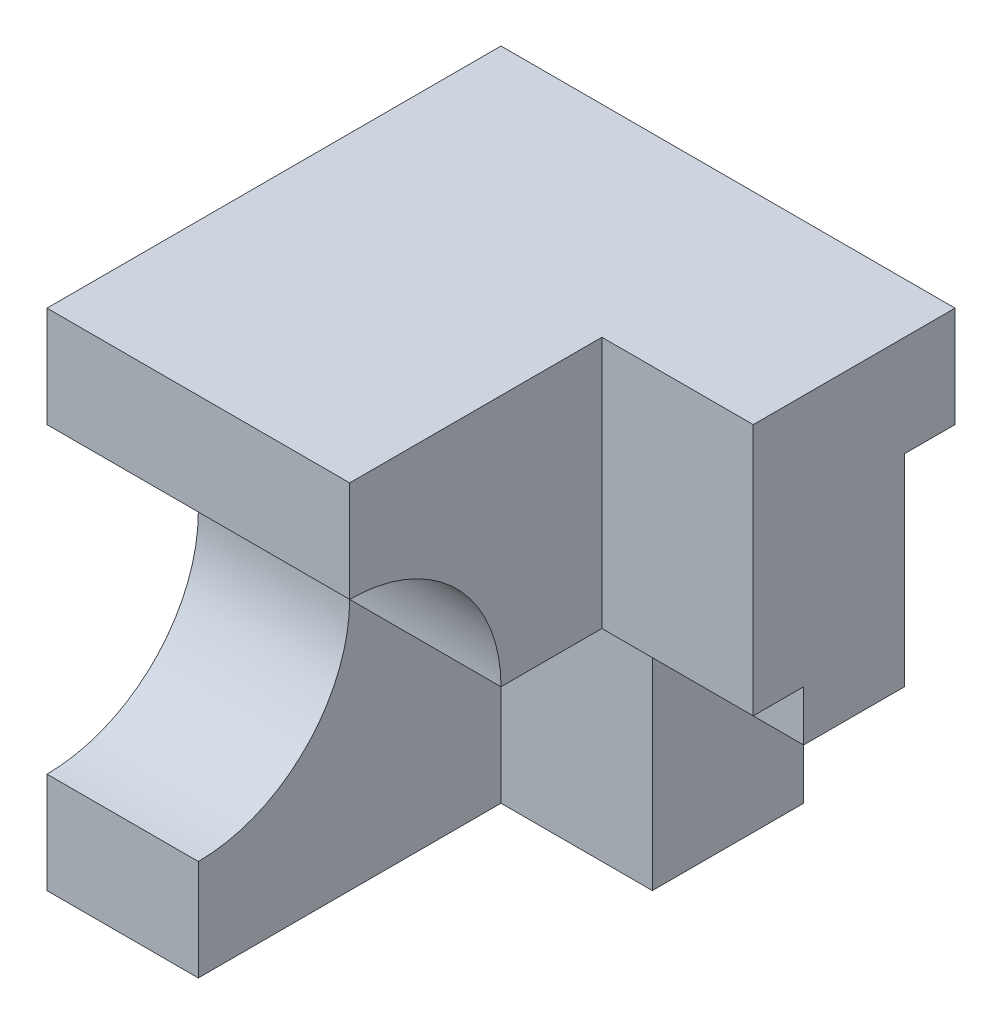
SolidWorks part; units mm, degrees
ref_plane "Front" through (0, 0, 0) normal (0, 0, 1) x (1, 0, 0)
ref_plane "Top" through (0, 0, 0) normal (0, 1, 0) x (1, 0, 0)
ref_plane "Right" through (0, 0, 0) normal (1, 0, 0) x (0, 0, -1)
sketch "Sketch1" plane through (0, 0, 0) normal (1, 0, 0) x (0, 0, -1)
  line L1 (4.5, -5) -> (-4.5, -5)
  line L2 (4.5, -5) -> (4.5, 5)
  line L3 (4.5, 5) -> (-4.5, 5)
  line L4 (-4.5, -5) -> (-4.5, 5)
  line L5 (4.5, -5) -> (-4.5, 5) construction
  line L6 (4.5, 5) -> (-4.5, -5) construction
  line L7 (4.5, -3) -> (3.5, -3)
  line L8 (4.5, -3) -> (4.5, 3)
  line L9 (4.5, 3) -> (3.5, 3)
  line L10 (3.5, -3) -> (3.5, 3)
  circle A0 centre (-4.5, 0) radius 3
  point P0 (0, 0)
  dimension "D2" = 6
  dimension "D1" = 9
  dimension "D3" = 2
  dimension "D4" = 2
  dimension "D5" = 10
  dimension "D6" = 1
extrude "Boss-Extrude1" add sketch "Sketch1" along normal blind 9 contours A0 L4 L1 L2 L7 L10 L9 L3
sketch "Sketch3" plane through (9, 0, 0) normal (1, 0, 0) x (0, 0, -1)
  line L0 (-1.5, 0) -> (0.5, 0)
  line L1 (0.5, 0) -> (0.5, 5)
  line L2 (1.5, -1) -> (3.5, -1)
  line L3 (1.5, -1) -> (1.5, -5)
  line L9 (-4.5, -3) -> (-4.5, -5)
  line L10 (-4.5, -5) -> (4.5, -5)
  line L11 (4.5, -5) -> (4.5, -3)
  line L12 (4.5, -3) -> (3.5, -3)
  line L13 (3.5, -3) -> (3.5, 3)
  line L14 (3.5, 3) -> (4.5, 3)
  line L15 (4.5, 3) -> (4.5, 5)
  line L16 (4.5, 5) -> (-4.5, 5)
  line L17 (-4.5, 5) -> (-4.5, 3)
  line L18 (-4.5, -3) -> (-4.5, -5)
  line L19 (-4.5, -5) -> (4.5, -5)
  line L20 (4.5, -5) -> (4.5, -3)
  line L21 (4.5, -3) -> (3.5, -3)
  line L22 (3.5, -3) -> (3.5, 3)
  line L23 (3.5, 3) -> (4.5, 3)
  line L24 (4.5, 3) -> (4.5, 5)
  line L25 (4.5, 5) -> (-4.5, 5)
  line L26 (-4.5, 5) -> (-4.5, 3)
  arc A1 (-4.5, -3) -> (-4.5, 3) centre (-4.5, 0) ccw
  arc A2 (-4.5, -3) -> (-4.5, 3) centre (-4.5, 0) ccw
  arc M13 (-4.5, 3) -> (-4.5, -3) centre (-4.5, 0) cw
  line M15 (-4.5, -5) -> (4.5, -5)
  line M16 (4.5, -5) -> (4.5, -3)
  line M17 (4.5, -3) -> (3.5, -3)
  line M18 (3.5, -3) -> (3.5, 3)
  line M21 (4.5, 5) -> (-4.5, 5)
  line M22 (-4.5, 5) -> (-4.5, 3)
  dimension "D2" = 2
  dimension "D3" = 4
  dimension "D1" = 0
extrude "Cut-Extrude1" cut sketch "Sketch3" against normal blind 3 contours L0 L1 M21 M22 M13 | L2 L3 M15 M16 M17 M18
sketch "Sketch5" plane through (9, 0, 0) normal (1, 0, 0) x (0, 0, -1)
  line L1 (-4.5, -5) -> (1.5, -5)
  line L2 (-4.5, -5) -> (-4.5, 0)
  line L3 (-4.5, 0) -> (1.5, 0)
  line L4 (1.5, -5) -> (1.5, 0)
  dimension "D1" = 6
  dimension "D2" = 5
extrude "Cut-Extrude2" cut sketch "Sketch5" against normal blind 6
